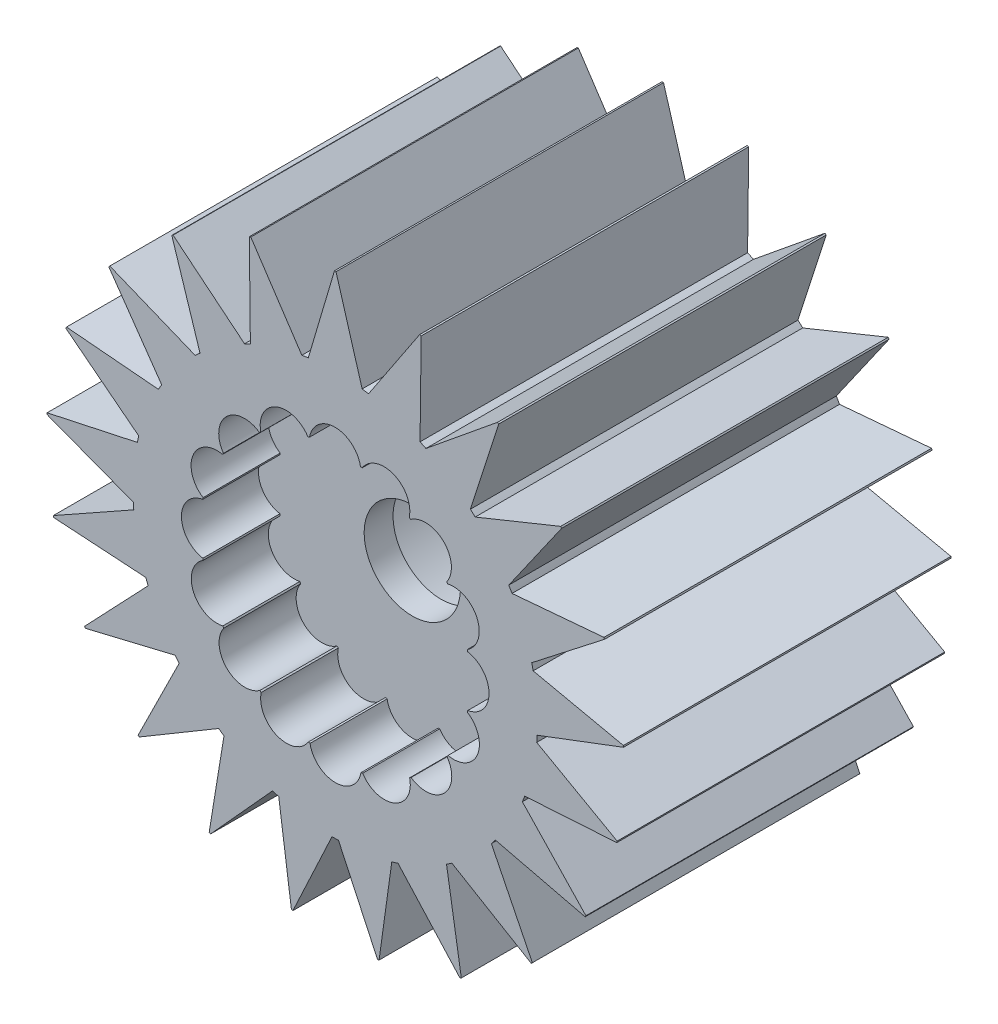
SolidWorks part; units mm, degrees
ref_plane "Front" through (0, 0, 0) normal (0, 0, 1) x (1, 0, 0)
ref_plane "Top" through (0, 0, 0) normal (0, 1, 0) x (1, 0, 0)
ref_plane "Right" through (0, 0, 0) normal (1, 0, 0) x (0, 0, -1)
sketch "草图1" plane through (0, 0, 0) normal (0, 0, 1) x (1, 0, 0)
  line L0 (-0.02, 7.5) -> (-0.7, 5.2031)
  line L1 (0.02, 7.5) -> (0.6984, 5.2033)
  line L2 (2.2298, 7.1609) -> (2.2011, 4.7663)
  line L3 (2.1915, 7.1727) -> (0.8647, 5.1783)
  line L4 (4.2414, 6.1855) -> (3.5082, 3.9057)
  line L5 (4.2084, 6.208) -> (2.3527, 4.6933)
  line L6 (5.8762, 4.6605) -> (4.5036, 2.6982)
  line L7 (5.8512, 4.6918) -> (3.6315, 3.7914)
  line L8 (6.9888, 2.7214) -> (5.0988, 1.2508)
  line L9 (6.9742, 2.7587) -> (4.5877, 2.5525)
  line L10 (7.4805, 0.5405) -> (5.241, -0.3076)
  line L11 (7.4775, 0.5804) -> (5.1363, 1.0869)
  line L12 (7.3075, -1.6884) -> (4.9175, -1.8388)
  line L13 (7.3164, -1.6494) -> (5.2284, -0.4754)
  line L14 (6.4852, -3.7673) -> (4.157, -3.2065)
  line L15 (6.5052, -3.7327) -> (4.856, -1.9953)
  line L16 (5.0866, -5.5115) -> (3.0272, -4.2894)
  line L17 (5.1159, -5.4843) -> (4.0522, -3.338)
  line L18 (3.2361, -6.7659) -> (1.6284, -4.9911)
  line L19 (3.2721, -6.7486) -> (2.8882, -4.3841)
  line L20 (1.098, -7.4192) -> (0.0849, -5.2493)
  line L21 (1.1376, -7.4132) -> (1.4677, -5.0407)
  line L22 (-1.1376, -7.4132) -> (-1.4662, -5.0411)
  line L23 (-1.098, -7.4192) -> (-0.0833, -5.2493)
  line L24 (-3.2721, -6.7486) -> (-2.8869, -4.385)
  line L25 (-3.2361, -6.7659) -> (-1.6269, -4.9916)
  line L26 (-5.1159, -5.4843) -> (-4.0512, -3.3393)
  line L27 (-5.0866, -5.5115) -> (-3.0259, -4.2903)
  line L28 (-6.5052, -3.7327) -> (-4.8554, -1.9968)
  line L29 (-6.4852, -3.7673) -> (-4.156, -3.2078)
  line L30 (-7.3164, -1.6494) -> (-5.2283, -0.4769)
  line L31 (-7.3075, -1.6884) -> (-4.9169, -1.8403)
  line L32 (-7.4775, 0.5804) -> (-5.1366, 1.0853)
  line L33 (-7.4805, 0.5405) -> (-5.2409, -0.3092)
  line L34 (-6.9742, 2.7587) -> (-4.5885, 2.5512)
  line L35 (-6.9888, 2.7214) -> (-5.0992, 1.2493)
  line L36 (-5.8512, 4.6918) -> (-3.6327, 3.7903)
  line L37 (-5.8762, 4.6605) -> (-4.5044, 2.6968)
  line L38 (-4.2084, 6.208) -> (-2.3541, 4.6926)
  line L39 (-4.2414, 6.1855) -> (-3.5094, 3.9047)
  line L40 (-2.1915, 7.1727) -> (-0.8663, 5.178)
  line L41 (-2.2298, 7.1609) -> (-2.2025, 4.7656)
  arc A0 (-0.7, 5.2031) -> (-0.8663, 5.178) centre (0, 0) ccw
  arc A2 (0.02, 7.5) -> (-0.02, 7.5) centre (0, 0) ccw
  arc A3 (2.2298, 7.1609) -> (2.1915, 7.1727) centre (0, 0) ccw
  arc A4 (4.2414, 6.1855) -> (4.2084, 6.208) centre (0, 0) ccw
  arc A5 (5.8762, 4.6605) -> (5.8512, 4.6918) centre (0, 0) ccw
  arc A6 (6.9888, 2.7214) -> (6.9742, 2.7587) centre (0, 0) ccw
  arc A7 (7.4805, 0.5405) -> (7.4775, 0.5804) centre (0, 0) ccw
  arc A8 (7.3075, -1.6884) -> (7.3164, -1.6494) centre (0, 0) ccw
  arc A9 (6.4852, -3.7673) -> (6.5052, -3.7327) centre (0, 0) ccw
  arc A10 (5.0866, -5.5115) -> (5.1159, -5.4843) centre (0, 0) ccw
  arc A11 (3.2361, -6.7659) -> (3.2721, -6.7486) centre (0, 0) ccw
  arc A12 (1.098, -7.4192) -> (1.1376, -7.4132) centre (0, 0) ccw
  arc A13 (-1.1376, -7.4132) -> (-1.098, -7.4192) centre (0, 0) ccw
  arc A14 (-3.2721, -6.7486) -> (-3.2361, -6.7659) centre (0, 0) ccw
  arc A15 (-5.1159, -5.4843) -> (-5.0866, -5.5115) centre (0, 0) ccw
  arc A16 (-6.5052, -3.7327) -> (-6.4852, -3.7673) centre (0, 0) ccw
  arc A17 (-7.3164, -1.6494) -> (-7.3075, -1.6884) centre (0, 0) ccw
  arc A18 (-7.4775, 0.5804) -> (-7.4805, 0.5405) centre (0, 0) ccw
  arc A19 (-6.9742, 2.7587) -> (-6.9888, 2.7214) centre (0, 0) ccw
  arc A20 (-5.8512, 4.6918) -> (-5.8762, 4.6605) centre (0, 0) ccw
  arc A21 (-4.2084, 6.208) -> (-4.2414, 6.1855) centre (0, 0) ccw
  arc A22 (-2.1915, 7.1727) -> (-2.2298, 7.1609) centre (0, 0) ccw
  arc A23 (-2.2025, 4.7656) -> (-2.3541, 4.6926) centre (0, 0) ccw
  arc A24 (-3.5094, 3.9047) -> (-3.6327, 3.7903) centre (0, 0) ccw
  arc A25 (0.8647, 5.1783) -> (0.6984, 5.2033) centre (0, 0) ccw
  arc A26 (2.3527, 4.6933) -> (2.2011, 4.7663) centre (0, 0) ccw
  arc A27 (3.6315, 3.7914) -> (3.5082, 3.9057) centre (0, 0) ccw
  arc A28 (-4.5044, 2.6968) -> (-4.5885, 2.5512) centre (0, 0) ccw
  arc A29 (-5.0992, 1.2493) -> (-5.1366, 1.0853) centre (0, 0) ccw
  arc A30 (-5.2409, -0.3092) -> (-5.2283, -0.4769) centre (0, 0) ccw
  arc A31 (-4.9169, -1.8403) -> (-4.8554, -1.9968) centre (0, 0) ccw
  arc A32 (-4.156, -3.2078) -> (-4.0512, -3.3393) centre (0, 0) ccw
  arc A33 (-3.0259, -4.2903) -> (-2.8869, -4.385) centre (0, 0) ccw
  arc A34 (-1.6269, -4.9916) -> (-1.4662, -5.0411) centre (0, 0) ccw
  arc A35 (-0.0833, -5.2493) -> (0.0849, -5.2493) centre (0, 0) ccw
  arc A36 (1.4677, -5.0407) -> (1.6284, -4.9911) centre (0, 0) ccw
  arc A37 (2.8882, -4.3841) -> (3.0272, -4.2894) centre (0, 0) ccw
  arc A38 (4.0522, -3.338) -> (4.157, -3.2065) centre (0, 0) ccw
  arc A39 (4.856, -1.9953) -> (4.9175, -1.8388) centre (0, 0) ccw
  arc A40 (5.2284, -0.4754) -> (5.241, -0.3076) centre (0, 0) ccw
  arc A41 (5.1363, 1.0869) -> (5.0988, 1.2508) centre (0, 0) ccw
  arc A42 (4.5877, 2.5525) -> (4.5036, 2.6982) centre (0, 0) ccw
  point P3 (0, 5.25)
  point P5 (0, 7.5)
  point P6 (-0.7, 5.2031)
  point P7 (0.6984, 5.2033)
  point P8 (-0.02, 7.5)
  point P9 (0.02, 7.5)
  point P95 (0, 0)
  dimension "D1" = 0.7
  dimension "D5" = 10.5
  dimension "D6" = 15
  dimension "D7" = 21
  dimension "D2" = 0.7
  dimension "D3" = 0.02
  dimension "D4" = 0.02
extrude "凸台-拉伸1" add sketch "草图1" along normal mid plane 8.5
sketch "草图2" plane through (0, 0, 0) normal (0, 0, 1) x (1, 0, 0)
  circle A0 centre (0, 0) radius 1.25
  dimension "D1" = 2.5
extrude "切除-拉伸1" cut sketch "草图2" against normal through all both and the other way through all
sketch "草图3" plane through (0, 0, 0) normal (0, 0, 1) x (1, 0, 0)
  circle A0 centre (0, 0) radius 3
  dimension "D1" = 6
extrude "切除-拉伸2" cut sketch "草图3" against normal blind 10 and the other way blind 1.5
sketch "草图5" plane through (0, 0, 0) normal (0, 0, 1) x (1, 0, 0)
  circle A0 centre (0, 0) radius 5
  circle A1 centre (0, 0) radius 7.8194
  dimension "D1" = 10
extrude "切除-拉伸4" [suppressed] cut sketch "草图5" against normal mid plane 5
sketch "草图6" plane through (0, 0, 0) normal (0, 0, 1) x (1, 0, 0)
  circle A0 centre (0, 0) radius 3.25
  circle A1 centre (0, 0) radius 8.2316
extrude "切除-拉伸5" [suppressed] cut sketch "草图6" along normal blind 1.5
sketch "草图7" plane through (0, 0, 0) normal (0, 0, 1) x (1, 0, 0)
  circle A0 centre (0, 0) radius 3.25
  circle A1 centre (0, 0) radius 7.4674
extrude "切除-拉伸6" [suppressed] cut sketch "草图7" against normal blind 2.5
sketch "草图8" plane through (0, 0, 4.25) normal (0, 0, 1) x (1, 0, 0)
  arc A0 (-0.6677, 3.4357) -> (-0.7112, 3.427) centre (0, 0) ccw
  arc A2 (-0.6677, 3.4357) -> (0.6544, 3.4383) centre (-0.0064, 3.3208) cw
  arc A3 (0.6979, 3.4297) -> (1.9204, 2.9261) centre (1.2649, 3.0705) cw
  arc A4 (1.9573, 2.9016) -> (2.894, 1.9685) centre (2.3436, 2.3527) cw
  arc A5 (2.9187, 1.9317) -> (3.427, 0.7112) centre (3.0656, 1.2768) cw
  arc A6 (3.4357, 0.6677) -> (3.4383, -0.6544) centre (3.3208, 0.0064) cw
  arc A7 (3.4297, -0.6979) -> (2.9261, -1.9204) centre (3.0705, -1.2649) cw
  arc A8 (2.9016, -1.9573) -> (1.9685, -2.894) centre (2.3527, -2.3436) cw
  arc A9 (1.9317, -2.9187) -> (0.7112, -3.427) centre (1.2768, -3.0656) cw
  arc A10 (0.6677, -3.4357) -> (-0.6544, -3.4383) centre (0.0064, -3.3208) cw
  arc A11 (-0.6979, -3.4297) -> (-1.9204, -2.9261) centre (-1.2649, -3.0705) cw
  arc A12 (-1.9573, -2.9016) -> (-2.894, -1.9685) centre (-2.3436, -2.3527) cw
  arc A13 (-2.9187, -1.9317) -> (-3.427, -0.7112) centre (-3.0656, -1.2768) cw
  arc A14 (-3.4357, -0.6677) -> (-3.4383, 0.6544) centre (-3.3208, -0.0064) cw
  arc A15 (-3.4297, 0.6979) -> (-2.9261, 1.9204) centre (-3.0705, 1.2649) cw
  arc A16 (-2.9016, 1.9573) -> (-1.9685, 2.894) centre (-2.3527, 2.3436) cw
  arc A17 (-1.9317, 2.9187) -> (-0.7112, 3.427) centre (-1.2768, 3.0656) cw
  arc A18 (0.6979, 3.4297) -> (0.6544, 3.4383) centre (0, 0) ccw
  arc A19 (1.9573, 2.9016) -> (1.9204, 2.9261) centre (0, 0) ccw
  arc A20 (2.9187, 1.9317) -> (2.894, 1.9685) centre (0, 0) ccw
  arc A21 (3.4357, 0.6677) -> (3.427, 0.7112) centre (0, 0) ccw
  arc A22 (-2.9016, 1.9573) -> (-2.9261, 1.9204) centre (0, 0) ccw
  arc A23 (-1.9317, 2.9187) -> (-1.9685, 2.894) centre (0, 0) ccw
  arc A24 (-3.4297, 0.6979) -> (-3.4383, 0.6544) centre (0, 0) ccw
  arc A25 (-3.4357, -0.6677) -> (-3.427, -0.7112) centre (0, 0) ccw
  arc A26 (-2.9187, -1.9317) -> (-2.894, -1.9685) centre (0, 0) ccw
  arc A27 (-1.9573, -2.9016) -> (-1.9204, -2.9261) centre (0, 0) ccw
  arc A28 (-0.6979, -3.4297) -> (-0.6544, -3.4383) centre (0, 0) ccw
  arc A29 (0.6677, -3.4357) -> (0.7112, -3.427) centre (0, 0) ccw
  arc A30 (1.9317, -2.9187) -> (1.9685, -2.894) centre (0, 0) ccw
  arc A31 (2.9016, -1.9573) -> (2.9261, -1.9204) centre (0, 0) ccw
  arc A32 (3.4297, -0.6979) -> (3.4383, -0.6544) centre (0, 0) ccw
  point P4 (0, 4)
  point P5 (-0.6677, 3.4357)
  point P6 (0.6544, 3.4383)
  point P56 (0, 0)
  dimension "D1" = 7
  dimension "D2" = 16
  dimension "D3" = 4
extrude "切除-拉伸7" cut sketch "草图8" against normal blind 2
